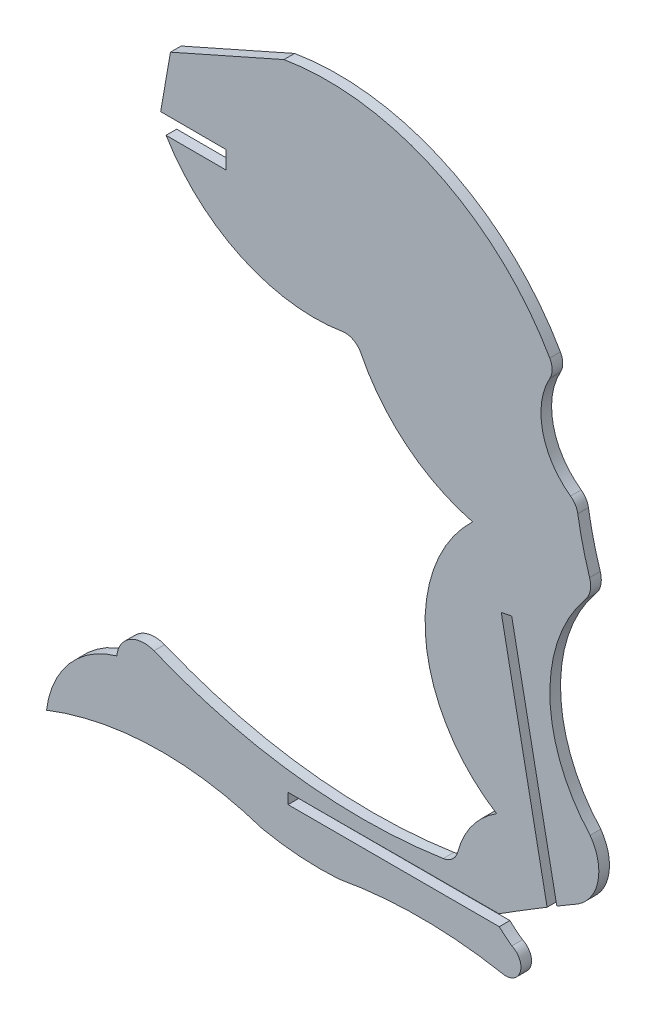
SolidWorks part; units mm, degrees
ref_plane "Front Plane" through (0, 0, 0) normal (0, 0, 1) x (1, 0, 0)
ref_plane "Top Plane" through (0, 0, 0) normal (0, 1, 0) x (1, 0, 0)
ref_plane "Right Plane" through (0, 0, 0) normal (1, 0, 0) x (0, 0, -1)
sketch "Sketch1" plane through (0, 0, 0) normal (0, 0, 1) x (1, 0, 0)
  line L0 (211.5237, 0) -> (211.5237, -2.54)
  line L1 (211.5237, -2.54) -> (202.9229, -2.5276)
  line L2 (211.5237, 0) -> (202.1482, 0.0136)
  line L3 (202.1482, 0.0136) -> (203.5536, 8.0958)
  line L4 (203.5536, 8.0958) -> (219.8014, 15.2991)
  line L5 (415.4863, -82.3745) -> (197.0188, -82.3745) construction
  line L6 (254.3833, -76.0279) -> (303.4816, -76.0279) construction
  line L7 (220.3898, -76.7899) -> (250.6325, -76.8046)
  line L8 (220.3898, -75.2659) -> (250.5814, -75.2295)
  line L9 (220.3898, -76.7899) -> (220.3898, -75.2659)
  line L10 (258.9931, -74.6908) -> (251.6638, -37.5426) construction
  line L13 (258.8717, -70.139) -> (252.4113, -37.3951)
  line L14 (257.4824, -70.9706) -> (250.9162, -37.6901)
  line L16 (252.4113, -37.3951) -> (250.9162, -37.6901)
  arc A0 (261.8737, -19.9728) -> (260.8385, -18.3088) centre (259.3663, -20.3787) ccw
  arc A1 (202.9229, -2.5276) -> (228.1529, -14.2377) centre (224.1751, 10.2265) ccw
  arc A2 (250.6325, -76.8046) -> (252.4387, -78.2887) centre (263.4288, -63.0719) ccw
  arc A3 (261.8737, -19.9728) -> (263.566, -27.0593) centre (310.5527, -12.093) ccw
  arc A4 (263.566, -27.0593) -> (262.9783, -30.0574) centre (260.5408, -28.0229) cw
  arc A5 (262.9783, -30.0574) -> (263.6411, -58.9643) centre (279.84, -44.1318) ccw
  arc A6 (263.6411, -58.9643) -> (261.9649, -68.3176) centre (258.2741, -62.8294) cw
  arc A7 (261.9649, -68.3176) -> (258.8717, -70.139) centre (442.886, -379.1145) ccw
  arc A8 (252.4387, -78.2887) -> (250.9939, -82.3745) centre (251.5567, -80.2752) cw
  arc A9 (250.9939, -82.3745) -> (227.7135, -82.3745) centre (239.3537, -145.668) ccw
  arc A10 (227.7135, -82.3745) -> (216.7163, -81.6275) centre (224.952, -41.7082) cw
  arc A11 (216.7163, -81.6275) -> (185.8079, -82.3745) centre (202.286, -124.366) ccw
  arc A12 (185.8079, -82.3745) -> (195.8716, -70.6097) centre (199.695, -84.067) cw
  arc A13 (195.8716, -70.6097) -> (201.1961, -67.3167) centre (199.7827, -70.9825) cw
  arc A14 (201.1961, -67.3167) -> (242.6147, -72.3626) centre (231.0139, 4.926) ccw
  arc A15 (244.6935, -70.4993) -> (242.6147, -72.3626) centre (242.2377, -69.8508) cw
  arc A16 (244.6935, -70.4993) -> (250.2499, -62.9779) centre (256.9409, -73.7338) cw
  arc A17 (250.2499, -62.9779) -> (246.8089, -28.5181) centre (261.9706, -44.4058) cw
  arc A18 (246.8089, -28.5181) -> (230.8326, -15.6092) centre (252.9806, -4.5391) cw
  arc A19 (219.8014, 15.2991) -> (257.8622, -2.6822) centre (225.9864, -20.8814) cw
  arc A20 (257.4824, -70.9706) -> (250.5814, -75.2295) centre (442.886, -379.1145) ccw
  arc A21 (228.1529, -14.2377) -> (230.8326, -15.6092) centre (228.5606, -16.7448) cw
  arc A22 (257.8622, -2.6822) -> (257.8749, -5.1784) centre (255.6564, -3.9416) cw
  arc A23 (257.8749, -5.1784) -> (260.8385, -18.3088) centre (266.6841, -10.0898) ccw
  point P48 (254.3833, -76.7899)
  point P49 (303.4816, -76.7899)
  point P50 (254.3833, -75.2659)
  point P51 (303.4816, -75.2659)
  point P56 (288.6923, -65.1275)
  point P58 (266.3502, -34.5573)
  point P59 (287.4619, -66.0268)
  point P60 (265.1198, -35.4565)
  dimension "D1" = 2.54
  dimension "D3" = 2.54
  dimension "D4" = 3.175
  dimension "D2" = 2.54
extrude "Boss-Extrude1" add sketch "Sketch1" along normal blind 1.524
